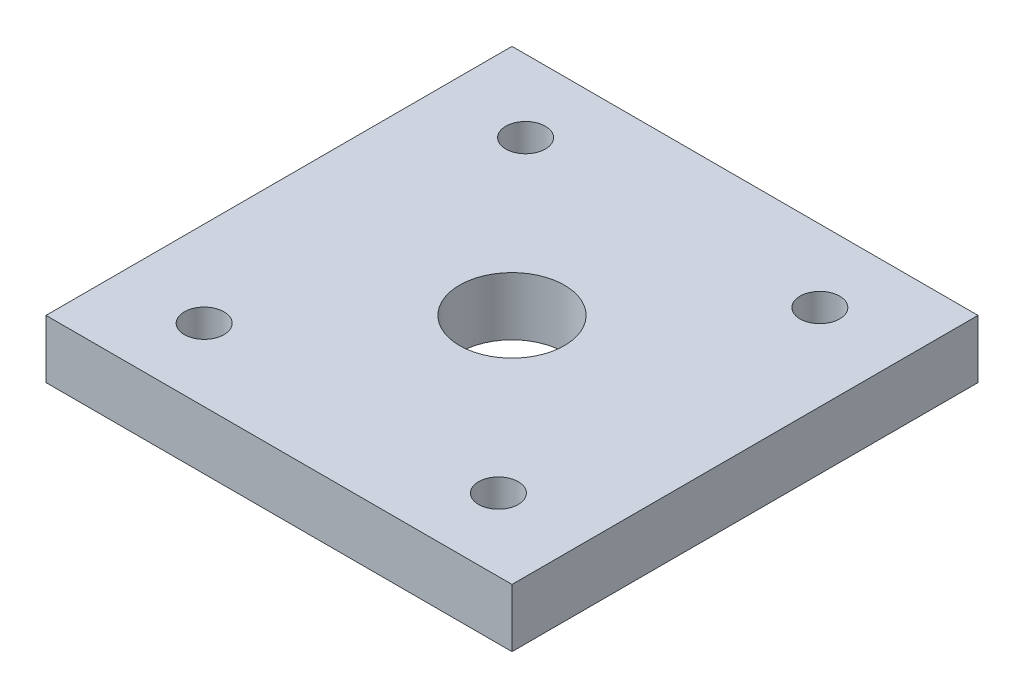
SolidWorks part; units mm, degrees
ref_plane "Front Plane" through (0, 0, 0) normal (0, 0, 1) x (1, 0, 0)
ref_plane "Top Plane" through (0, 0, 0) normal (0, 1, 0) x (1, 0, 0)
ref_plane "Right Plane" through (0, 0, 0) normal (1, 0, 0) x (0, 0, -1)
sketch "Croquis1" plane through (0, 0, 0) normal (0, 1, 0) x (1, 0, 0)
  line L1 (-20, 20) -> (20, 20)
  line L2 (-20, 20) -> (-20, -20)
  line L3 (-20, -20) -> (20, -20)
  line L4 (20, 20) -> (20, -20)
  line L5 (-20, 20) -> (20, -20) construction
  line L6 (-20, -20) -> (20, 20) construction
  circle A0 centre (0, 0) radius 4.5
  point P0 (0, 0)
  dimension "D3" = 9
  dimension "D1" = 40
  dimension "D2" = 40
extrude "Saliente-Extruir1" add sketch "Croquis1" along normal blind 5
sketch "Croquis2" plane through (0, 0, 0) normal (0, -1, 0) x (1, 0, 0)
  circle A0 centre (12.6288, -13.7953) radius 1.7
  circle A1 centre (12.6288, 13.7953) radius 1.7
  circle A2 centre (-12.6288, 13.7953) radius 1.7
  circle A3 centre (-12.6288, -13.7953) radius 1.7
extrude "Cortar-Extruir1" cut sketch "Croquis2" against normal blind 10
